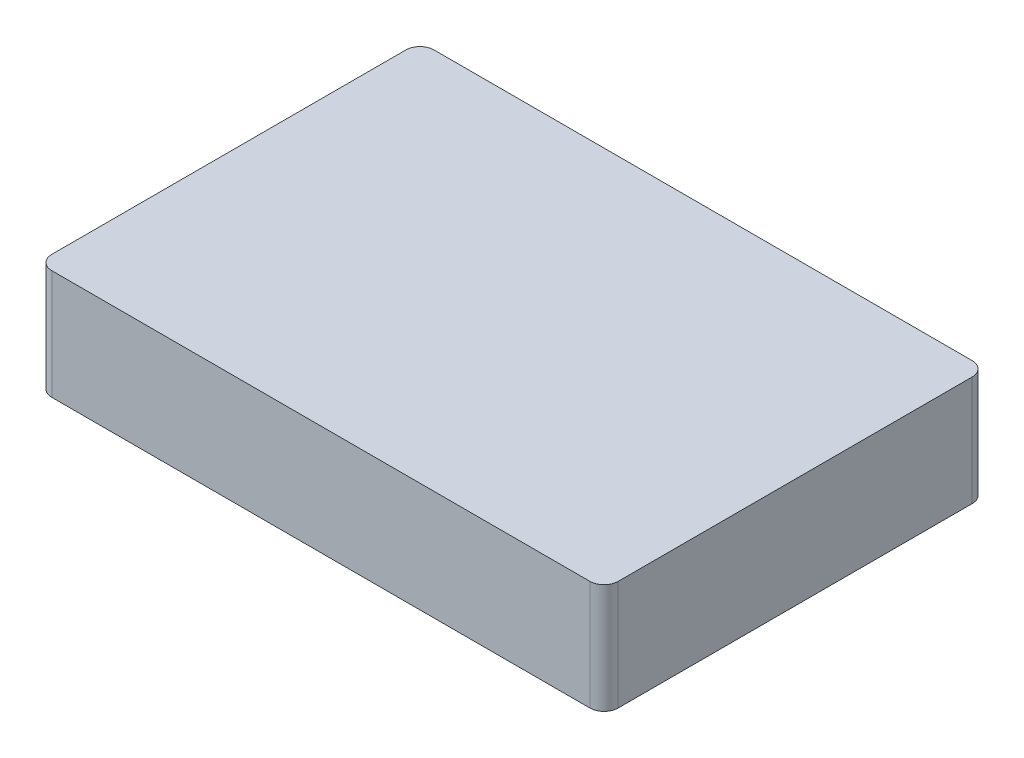
SolidWorks part; units mm, degrees
ref_plane "Front Plane" through (0, 0, 0) normal (0, 0, 1) x (1, 0, 0)
ref_plane "Top Plane" through (0, 0, 0) normal (0, 1, 0) x (1, 0, 0)
ref_plane "Right Plane" through (0, 0, 0) normal (1, 0, 0) x (0, 0, -1)
sketch "Sketch1" plane through (0, 0, 0) normal (0, 1, 0) x (1, 0, 0)
  line L1 (0, 0) -> (80, 0)
  line L2 (0, 0) -> (0, 54)
  line L3 (0, 54) -> (80, 54)
  line L4 (80, 0) -> (80, 54)
  dimension "D1" = 80
  dimension "D2" = 54
extrude "Boss-Extrude2" add sketch "Sketch1" along normal blind 15.5
fillet "Fillet1" radius 2 4 edges at (0, 7.75, -54) (0, 7.75, 0) (80, 7.75, -54) (80, 7.75, 0)
